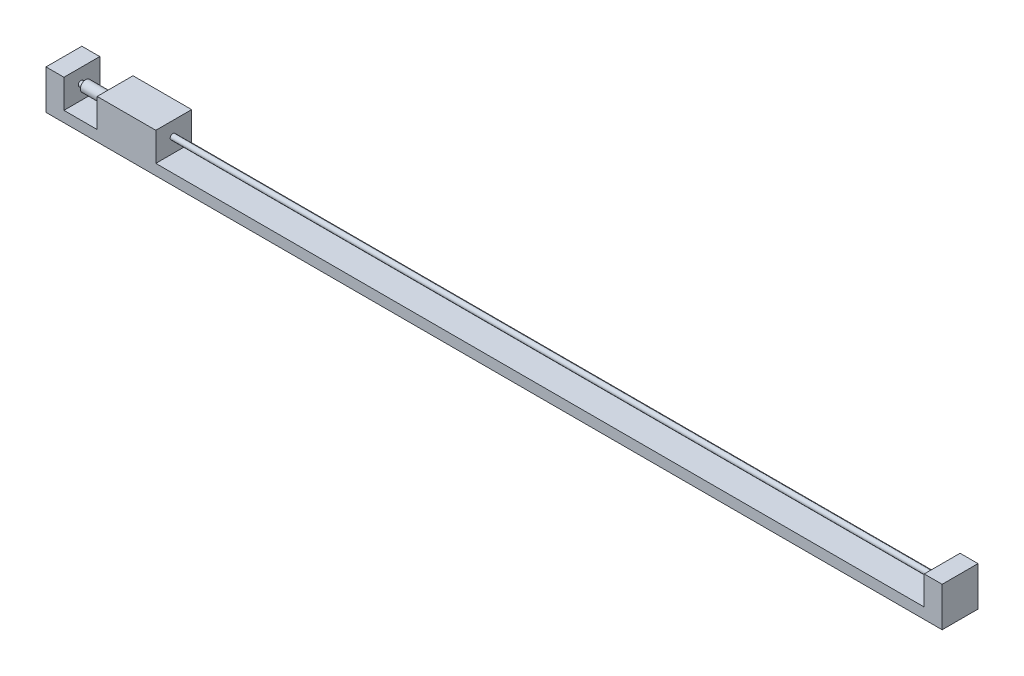
SolidWorks part; units mm, degrees
ref_plane "Front Plane" through (0, 0, 0) normal (0, 0, 1) x (1, 0, 0)
ref_plane "Top Plane" through (0, 0, 0) normal (0, 1, 0) x (1, 0, 0)
ref_plane "Right Plane" through (0, 0, 0) normal (1, 0, 0) x (0, 0, -1)
sketch "Sketch2" plane through (0, 0, 0) normal (0, 1, 0) x (1, 0, 0)
  line L1 (0, 0) -> (250, 0)
  line L2 (0, 0) -> (0, 10)
  line L3 (0, 10) -> (250, 10)
  line L4 (250, 0) -> (250, 10)
  dimension "D1" = 250
  dimension "D2" = 10
extrude "Boss-Extrude1" add sketch "Sketch2" along normal blind 3
sketch "Sketch3" plane through (0, 3, 0) normal (0, 1, 0) x (1, 0, 0)
  line L0 (250, 10) -> (0, 10) construction
  line L1 (0, 0) -> (5, 0)
  line L2 (0, 0) -> (0, 10)
  line L3 (0, 10) -> (5, 10)
  line L4 (5, 0) -> (5, 10)
  line L5 (0, 0) -> (250, 0) construction
  line L6 (250, 10) -> (245, 10)
  line L7 (250, 10) -> (250, 0)
  line L8 (250, 0) -> (245, 0)
  line L9 (245, 10) -> (245, 0)
  dimension "D1" = 5
  dimension "D2" = 5
extrude "Boss-Extrude2" add sketch "Sketch3" along normal blind 8
sketch "Sketch4" plane through (5, 0, 0) normal (1, 0, 0) x (0, 0, -1)
  circle A0 centre (4.7549, 7.1008) radius 0.75
  dimension "D1" = 1.5
extrude "Boss-Extrude3" add sketch "Sketch4" along normal up to next
sketch "Sketch5" plane through (0, 3, 0) normal (0, 1, 0) x (1, 0, 0)
  line L0 (245, 10) -> (5, 10) construction
  line L1 (14.2707, 10) -> (30.6304, 10)
  line L2 (14.2707, 10) -> (14.2707, 0)
  line L3 (14.2707, 0) -> (30.6304, 0)
  line L4 (30.6304, 10) -> (30.6304, 0)
  line L5 (5, 0) -> (245, 0) construction
extrude "Boss-Extrude4" add sketch "Sketch5" along normal blind 8
sketch "Sketch6" plane through (14.2707, 0, 0) normal (-1, 0, 0) x (0, 0, 1)
  circle A0 centre (-4.8009, 7.162) radius 1.1534
  circle A1 centre (-4.8009, 7.162) radius 1.4956
extrude "Boss-Extrude5" add sketch "Sketch6" along normal blind 8
